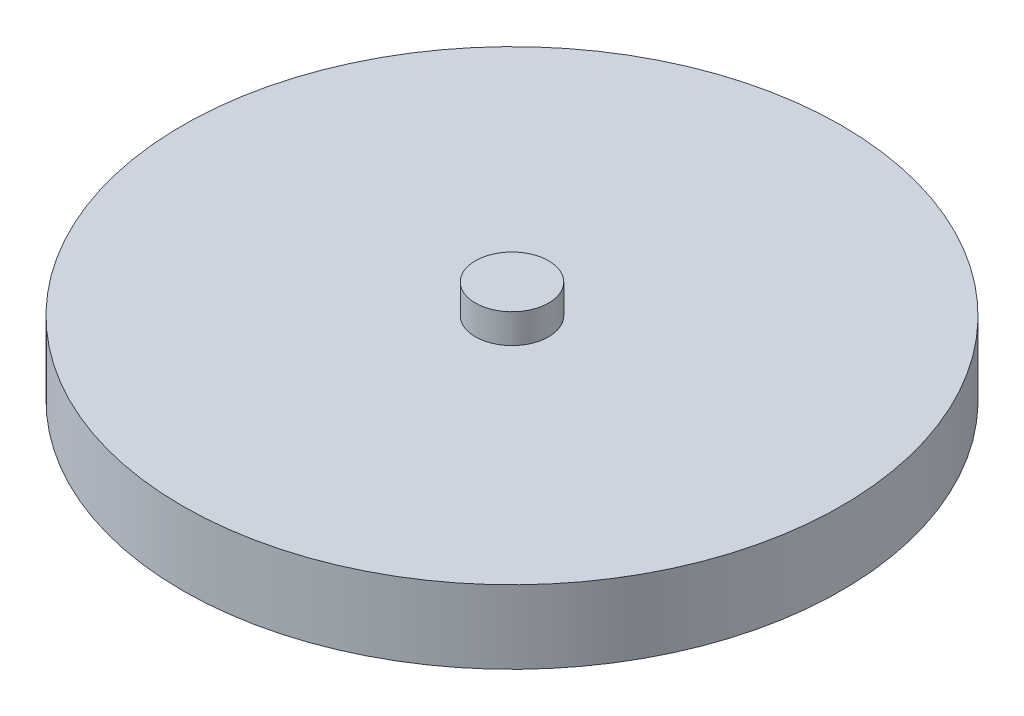
SolidWorks part; units mm, degrees
ref_plane "Front Plane" through (0, 0, 0) normal (0, 0, 1) x (1, 0, 0)
ref_plane "Top Plane" through (0, 0, 0) normal (0, 1, 0) x (1, 0, 0)
ref_plane "Right Plane" through (0, 0, 0) normal (1, 0, 0) x (0, 0, -1)
sketch "Sketch1" plane through (0, 0, 0) normal (0, 1, 0) x (1, 0, 0)
  circle A0 centre (0, 0) radius 22.5
  dimension "D1" = 45
extrude "Boss-Extrude1" add sketch "Sketch1" along normal blind 5
sketch "Sketch2" plane through (0, 5, 0) normal (0, 1, 0) x (1, 0, 0)
  circle A0 centre (0, 0) radius 2.5
  dimension "D1" = 5
extrude "Boss-Extrude2" add sketch "Sketch2" along normal blind 2
